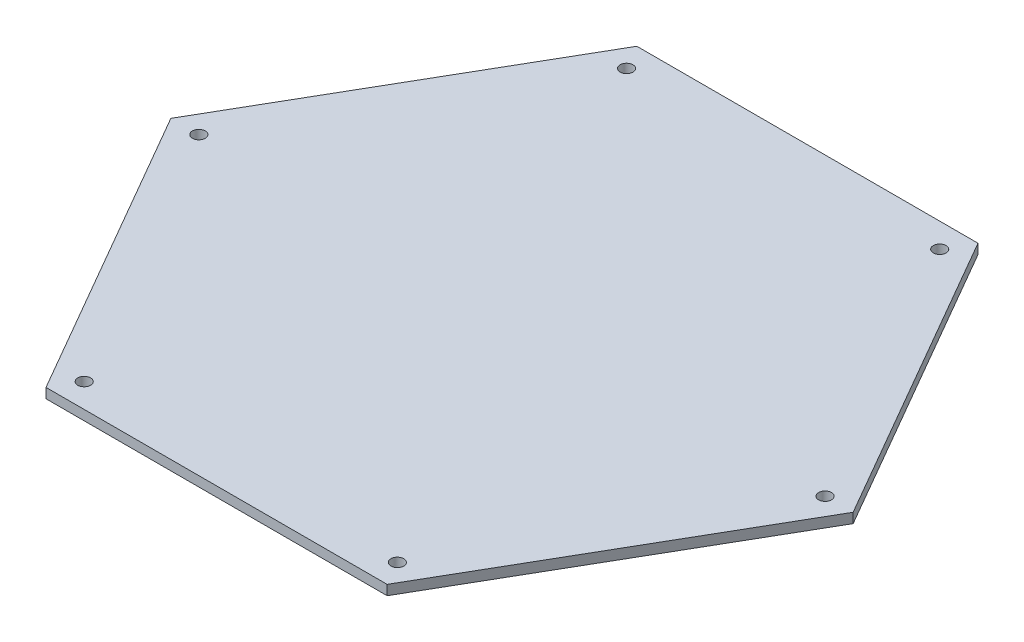
SolidWorks part; units mm, degrees
ref_plane "Front Plane" through (0, 0, 0) normal (0, 0, 1) x (1, 0, 0)
ref_plane "Top Plane" through (0, 0, 0) normal (0, 1, 0) x (1, 0, 0)
ref_plane "Right Plane" through (0, 0, 0) normal (1, 0, 0) x (0, 0, -1)
sketch "Sketch1" plane through (0, 0, 0) normal (0, 1, 0) x (1, 0, 0)
  line L0 (0, -76.0095) -> (0, 76.0095) construction
  line L1 (43.8841, -76.0095) -> (87.7682, 0)
  line L2 (87.7682, 0) -> (43.8841, 76.0095)
  line L3 (43.8841, 76.0095) -> (-43.8841, 76.0095)
  line L4 (-43.8841, 76.0095) -> (-87.7682, 0)
  line L5 (-87.7682, 0) -> (-43.8841, -76.0095)
  line L6 (-43.8841, -76.0095) -> (43.8841, -76.0095)
  circle A0 centre (0, 0) radius 76.0095 construction
  dimension "D1" = 152.019
extrude "Boss-Extrude1" add sketch "Sketch1" along normal blind 2.54
sketch "Sketch2" plane through (0, 2.54, 0) normal (0, 1, 0) x (1, 0, 0)
  line L0 (-41.0901, 71.1702) -> (-43.8841, 76.0095) construction
  line L1 (-41.0901, 71.1702) -> (43.8841, -76.0095) construction
  circle A0 centre (-40.2646, 69.7403) radius 1.651
  dimension "D1" = 3.302
  dimension "D2" = 5.588
extrude "Cut-Extrude1" cut sketch "Sketch2" against normal through all
pattern_circular "CirPattern1" count 6 over 360 about axis through (0.0172, 0, 0.0299) along (0, 1, 0) of "Cut-Extrude1"
